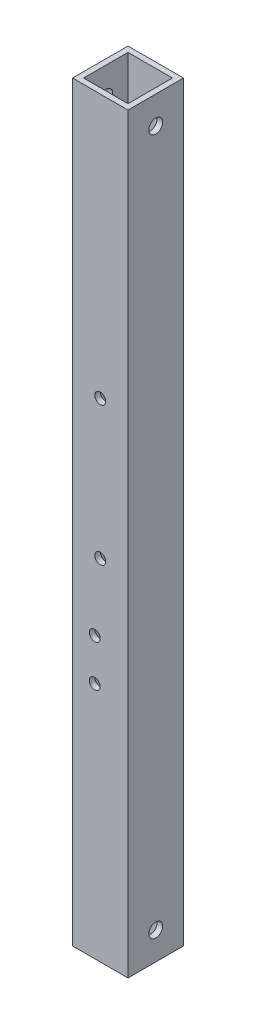
SolidWorks part; units mm, degrees
material "6061-T6 (SS)"
ref_plane "Front Plane" through (0, 0, 0) normal (0, 0, 1) x (1, 0, 0)
ref_plane "Top Plane" through (0, 0, 0) normal (0, 1, 0) x (1, 0, 0)
ref_plane "Right Plane" through (0, 0, 0) normal (1, 0, 0) x (0, 0, -1)
sketch "Sketch1" plane through (0, 0, 0) normal (0, 1, 0) x (1, 0, 0)
  line L1 (0, 0) -> (25.4, 0)
  line L2 (0, 0) -> (0, 25.4)
  line L3 (0, 25.4) -> (25.4, 25.4)
  line L4 (25.4, 0) -> (25.4, 25.4)
  dimension "D1" = 25.4
  dimension "D2" = 25.4
extrude "Extrude-Thin1" add sketch "Sketch1" along normal blind 344.17 thin thin type one direction reverse wall 2.54
sketch "Sketch2" plane through (0, 0, -25.4) normal (0, 0, -1) x (-1, 0, 0)
  circle A0 centre (-10.16, 109.1191) radius 2.4892 construction
  circle A1 centre (-10.16, 128.1691) radius 2.4892 construction
  circle A2 centre (-12.7, 160.02) radius 2.4892 construction
  circle A3 centre (-12.7, 223.52) radius 2.4892 construction
  circle A4 centre (-10.16, 109.1191) radius 2.4892
  circle A5 centre (-10.16, 128.1691) radius 2.4892
  circle A6 centre (-12.7, 160.02) radius 2.4892
  circle A7 centre (-12.7, 223.52) radius 2.4892
extrude "Cut-Extrude1" cut sketch "Sketch2" against normal through all
sketch "Sketch3" plane through (0, 0, 0) normal (0, 0, 1) x (1, 0, 0)
  circle A0 centre (12.7, 12.7) radius 2.4892 construction
  circle A1 centre (12.7, 25.4) radius 2.4892 construction
  circle A2 centre (12.7, 38.1) radius 2.4892 construction
  circle A3 centre (12.7, 50.8) radius 2.4892 construction
  circle A4 centre (12.7, 331.47) radius 2.4892 construction
  circle A5 centre (12.7, 318.77) radius 2.4892 construction
  circle A6 centre (12.7, 306.07) radius 2.4892 construction
  circle A7 centre (12.7, 293.37) radius 2.4892 construction
  circle A8 centre (12.7, 12.7) radius 2.4892
  circle A9 centre (12.7, 25.4) radius 2.4892
  circle A10 centre (12.7, 38.1) radius 2.4892
  circle A11 centre (12.7, 50.8) radius 2.4892
  circle A12 centre (12.7, 331.47) radius 2.4892
  circle A13 centre (12.7, 318.77) radius 2.4892
  circle A14 centre (12.7, 306.07) radius 2.4892
  circle A15 centre (12.7, 293.37) radius 2.4892
extrude "Cut-Extrude2" [suppressed] cut sketch "Sketch3" against normal through all
sketch "Sketch4" plane through (0, 0, 0) normal (-1, 0, 0) x (0, 0, 1)
  line L3 (0, 344.17) -> (0, 0) construction
  line L4 (-12.7, 0) -> (-12.7, 12.7) construction
  line L5 (-25.4, 0) -> (0, 0) construction
  line L6 (-12.7, 12.7) -> (0, 12.7) construction
  line L7 (-12.7, 344.17) -> (-12.7, 331.47) construction
  line L8 (-25.4, 344.17) -> (0, 344.17) construction
  line L9 (-12.7, 331.47) -> (-25.4, 331.47) construction
  line L10 (-25.4, 344.17) -> (-25.4, 0) construction
  circle A1 centre (-12.7, 12.7) radius 3.175
  circle A3 centre (-12.7, 331.47) radius 3.175
  dimension "D1" = 6.35
  dimension "D2" = 6.35
extrude "Cut-Extrude3" cut sketch "Sketch4" against normal through all
